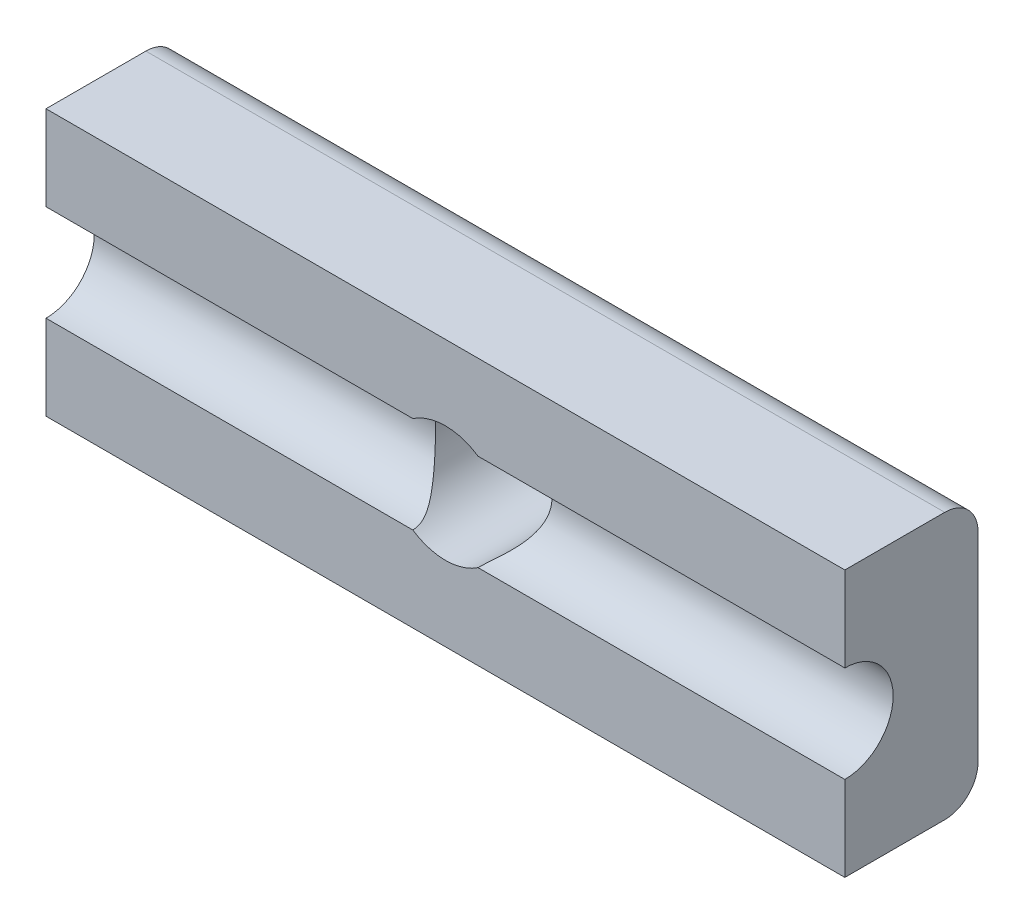
SolidWorks part; units mm, degrees
ref_plane "Front Plane" through (0, 0, 0) normal (0, 0, 1) x (1, 0, 0)
ref_plane "Top Plane" through (0, 0, 0) normal (0, 1, 0) x (1, 0, 0)
ref_plane "Right Plane" through (0, 0, 0) normal (1, 0, 0) x (0, 0, -1)
sketch "Sketch2" plane through (0, 0, 0) normal (0, 0, 1) x (1, 0, 0)
  line L1 (-5.0427, 4) -> (18.9573, 4)
  line L2 (-5.0427, 4) -> (-5.0427, -4)
  line L3 (-5.0427, -4) -> (18.9573, -4)
  line L4 (18.9573, 4) -> (18.9573, -4)
  dimension "D1" = 8
  dimension "D2" = 24
extrude "Boss-Extrude1" add sketch "Sketch2" along normal blind 4
sketch "Sketch3" plane through (0, 0, 4) normal (0, 0, 1) x (1, 0, 0)
  line L0 (-5.0427, 4) -> (-5.0427, -4) construction
  line L1 (18.9573, 4) -> (-5.0427, 4) construction
  circle A0 centre (6.9573, 0) radius 1.75
  point P2 (0, 0)
  point P5 (-5.0427, 0)
  point P8 (6.9573, 4)
  dimension "D1" = 3.5
extrude "Cut-Extrude1" cut sketch "Sketch3" against normal blind 5
sketch "Sketch4" plane through (-5.0427, 0, 0) normal (-1, 0, 0) x (0, 0, 1)
  line L0 (4, 4) -> (4, -4) construction
  circle A0 centre (4, 0) radius 1.45
  dimension "D1" = 2.9
extrude "Cut-Extrude2" cut sketch "Sketch4" against normal blind 44
fillet "Fillet1" radius 1 2 edges at (6.9573, -4, 0) (6.9573, 4, 0)
